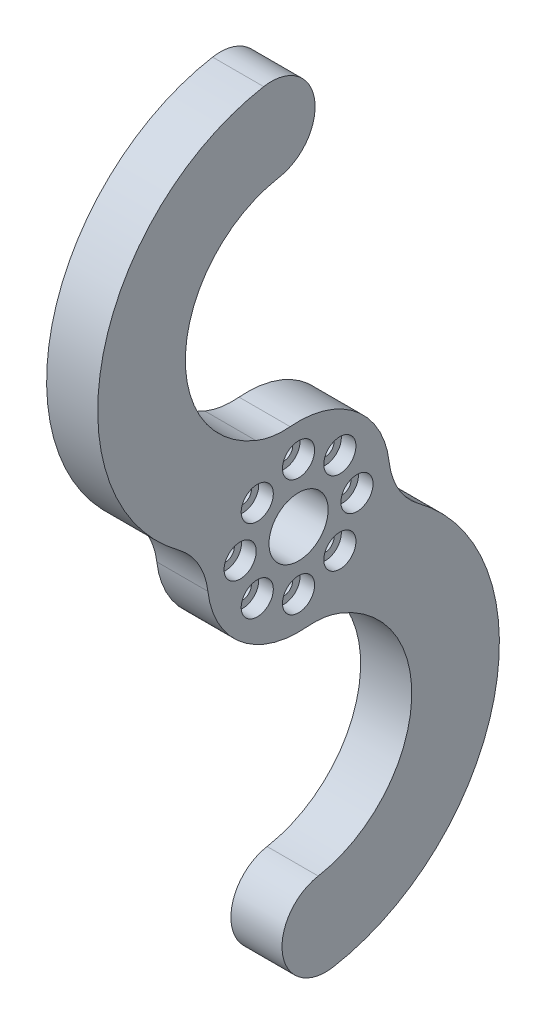
SolidWorks part; units mm, degrees
ref_plane "Front" through (0, 0, 0) normal (0, 0, 1) x (1, 0, 0)
ref_plane "Top" through (0, 0, 0) normal (0, 1, 0) x (1, 0, 0)
ref_plane "Right" through (0, 0, 0) normal (1, 0, 0) x (0, 0, -1)
sketch "Sketch1" plane through (0, 0, 0) normal (1, 0, 0) x (0, 0, -1)
  line L0 (3.7334, -48.6734) -> (0, -27.5) construction
  line L1 (0, -27.5) -> (0, 0) construction
  line L2 (0, 0) -> (12.1729, -2.8409) construction
  line L3 (0, 0) -> (-12.1729, 2.8409) construction
  circle A1 centre (0, 0) radius 12.5
  arc A4 (2.6915, -42.7645) -> (2.6182, -12.2227) centre (0, -27.5) ccw
  arc A5 (2.6915, -42.7645) -> (4.7753, -54.5822) centre (3.7334, -48.6734) ccw
  circle A6 centre (0, 0) radius 8 construction
  circle A7 centre (0, 0) radius 4.05
  circle A8 centre (0, 0) radius 54.7907 construction
  arc A9 (4.7753, -54.5822) -> (12.1729, -2.8409) centre (0, -27.5) ccw
  circle A10 centre (0, -27.5) radius 27.5 construction
  circle A11 centre (0, -27.5) radius 15.5 construction
  arc A12 (-2.6915, 42.7645) -> (-4.7753, 54.5822) centre (-3.7334, 48.6734) ccw
  arc A13 (-2.6915, 42.7645) -> (-2.6182, 12.2227) centre (0, 27.5) ccw
  arc A14 (-4.7753, 54.5822) -> (-12.1729, 2.8409) centre (0, 27.5) ccw
  point P8 (-2.3269, 12.2815)
  dimension "D1" = 55
  dimension "D2" = 25
  dimension "D5" = 16
  dimension "D6" = 8.1
  dimension "D7" = 109.5814
  dimension "D8" = 2
  dimension "D3" = 12
  dimension "D4" = 170
extrude "Boss-Extrude1" add sketch "Sketch1" along normal blind 7
fillet "Fillet1" radius 10 4 edges at (3.5, -12.2227, -2.6182) (3.5, -2.8409, -12.1729) (3.5, 2.8409, 12.1729) (3.5, 12.2227, 2.6182)
hole_wizard "CBORE for M2 SHCS1" positions "Sketch2" profile "Sketch3" counterbore size "M2" standard "ANSI Metric" end condition through all
sketch "Sketch2" plane through (7, 0, 0) normal (1, 0, 0) x (0, 0, -1)
  line L0 (0, 0) -> (0, 8) construction
  circle A0 centre (0, 0) radius 8 construction
  point P5 (0, 8)
  point P10 (5.6569, 5.6569)
  point P11 (8, 0)
  point P12 (5.6569, -5.6569)
  point P13 (0, -8)
  point P14 (-5.6569, -5.6569)
  point P15 (-8, 0)
  point P16 (-5.6569, 5.6569)
  dimension "D1" = 16
  dimension "D2" = 8
sketch "Sketch3" plane through (7, 5.6569, 5.6569) normal (0, 1, 0) x (0, 0, -1)
  line L0 (0, 0) -> (0, 7)
  line L1 (0, 7) -> (1.2, 7)
  line L3 (1.2, 7) -> (1.2, 2)
  line L4 (1.2, 2) -> (2.2, 2)
  line L5 (2.2, 2) -> (2.2, 0)
  line L7 (2.2, 0) -> (0, 0)
  line L11 (0, -6.35) -> (0, 107.95) construction
  dimension "Thru Hole Dia." = 2.4
  dimension "Thru Hole Depth" = 7
  dimension "C'Bore Dia." = 4.4
  dimension "C'Bore Depth" = 2
chamfer "Chamfer1" [suppressed] distance 1 angle 45
sketch "Sketch4" [suppressed] plane through (7, 0, 0) normal (1, 0, 0) x (0, 0, -1)
  line L0 (-0.33, -41.1409) -> (-2.5617, -43.5943)
  arc A0 (2.3269, -38.5964) -> (4.4107, -50.4141) centre (3.3688, -44.5053) ccw construction
  arc A1 (2.3269, -38.5964) -> (4.4107, -50.4141) centre (3.3688, -44.5053) ccw
  arc A2 (2.3269, -38.5964) -> (2.5307, -12.2411) centre (0, -25.4) ccw construction
  arc A3 (2.3269, -38.5964) -> (8.5902, -35.6844) centre (0, -25.4) ccw
  arc A4 (4.4107, -50.4141) -> (12.1157, -3.0758) centre (0, -25.4) ccw construction
  arc A5 (4.4107, -50.4141) -> (16.283, -44.8942) centre (0, -25.4) ccw
  arc A6 (16.283, -44.8942) -> (8.5902, -35.6844) centre (12.4366, -40.2893) ccw
  arc A7 (2.5005, -39.5812) -> (4.237, -49.4293) centre (3.3688, -44.5053) ccw construction
  arc A8 (2.5005, -39.5812) -> (4.237, -49.4293) centre (3.3688, -44.5053) ccw
  arc A9 (2.5005, -39.5812) -> (7.0699, -12.855) centre (0, -25.4) ccw construction
  arc A10 (2.5005, -39.5812) -> (7.0699, -12.855) centre (0, -25.4) ccw
  arc A11 (2.3269, -38.5964) -> (4.4107, -50.4141) centre (3.3688, -44.5053) ccw construction
  arc M7 (7.0699, -12.855) -> (2.5005, -39.5812) centre (0, -25.4) cw
  arc M8 (2.5005, -39.5812) -> (4.237, -49.4293) centre (3.3688, -44.5053) ccw
  arc M9 (4.237, -49.4293) -> (15.4469, -6.5121) centre (0, -25.4) ccw
  dimension "D1" = 10
extrude "Boss-Extrude2" [suppressed] add sketch "Sketch4" against normal up to surface (7 mm away) contours A6 M9 M7 M8 | A5 A6 L0 A1 M9 M8
fillet "Fillet2" [suppressed] radius 3
